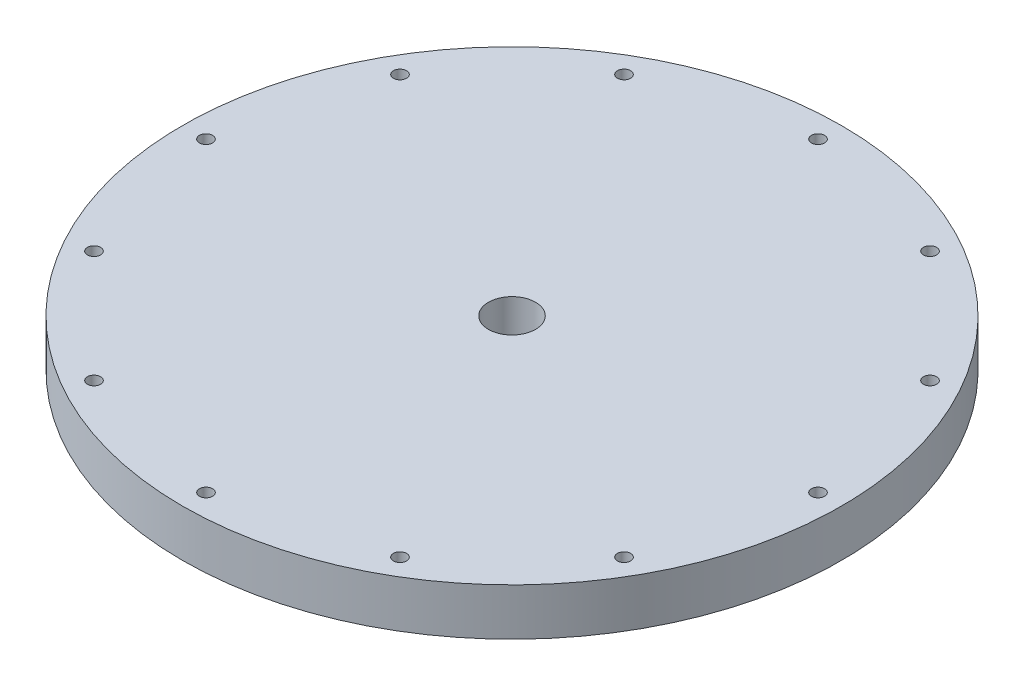
SolidWorks part; units mm, degrees
material "6061-T6 (SS)"
ref_plane "Front Plane" through (0, 0, 0) normal (0, 0, 1) x (1, 0, 0)
ref_plane "Top Plane" through (0, 0, 0) normal (0, 1, 0) x (1, 0, 0)
ref_plane "Right Plane" through (0, 0, 0) normal (1, 0, 0) x (0, 0, -1)
sketch "Sketch1" plane through (0, 0, 0) normal (0, 0, 1) x (1, 0, 0)
  line L0 (0, 49.9671) -> (0, -61.2678) construction
sketch "Sketch2" plane through (0, 0, 0) normal (0, 0, 1) x (1, 0, 0)
  line L0 (-38.1, -5.1478) -> (-44.45, -5.1478)
  line L1 (-3.175, 1.2022) -> (-44.45, 1.2022)
  line L2 (-3.175, 1.2022) -> (-3.175, -5.1478)
  line L3 (-3.175, -5.1478) -> (-34.925, -5.1478)
  line L4 (-44.45, 1.2022) -> (-44.45, -5.1478)
  line L5 (-38.1, -5.1478) -> (-34.925, -5.1478)
  dimension "D1" = 3.175
  dimension "D2" = 41.275
  dimension "D5" = 6.35
revolve "Revolve1" add sketch "Sketch2" angle 360 about L0
sketch "Sketch5" plane through (0, 1.2022, 0) normal (0, 1, 0) x (1, 0, 0)
  circle A0 centre (0, 0) radius 41.275 construction
  circle A1 centre (-41.275, 0) radius 0.889
  circle A2 centre (-35.7452, 20.6375) radius 0.889
  circle A3 centre (-20.6375, 35.7452) radius 0.889
  circle A4 centre (0, 41.275) radius 0.889
  circle A5 centre (20.6375, 35.7452) radius 0.889
  circle A6 centre (35.7452, 20.6375) radius 0.889
  circle A7 centre (41.275, 0) radius 0.889
  circle A8 centre (35.7452, -20.6375) radius 0.889
  circle A9 centre (20.6375, -35.7452) radius 0.889
  circle A10 centre (0, -41.275) radius 0.889
  circle A11 centre (-20.6375, -35.7452) radius 0.889
  circle A12 centre (-35.7452, -20.6375) radius 0.889
  point P30 (0, 0)
  dimension "D1" = 82.55
  dimension "D2" = 1.778
  dimension "D3" = 12
extrude "Cut-Extrude1" cut sketch "Sketch5" against normal blind 12.7
